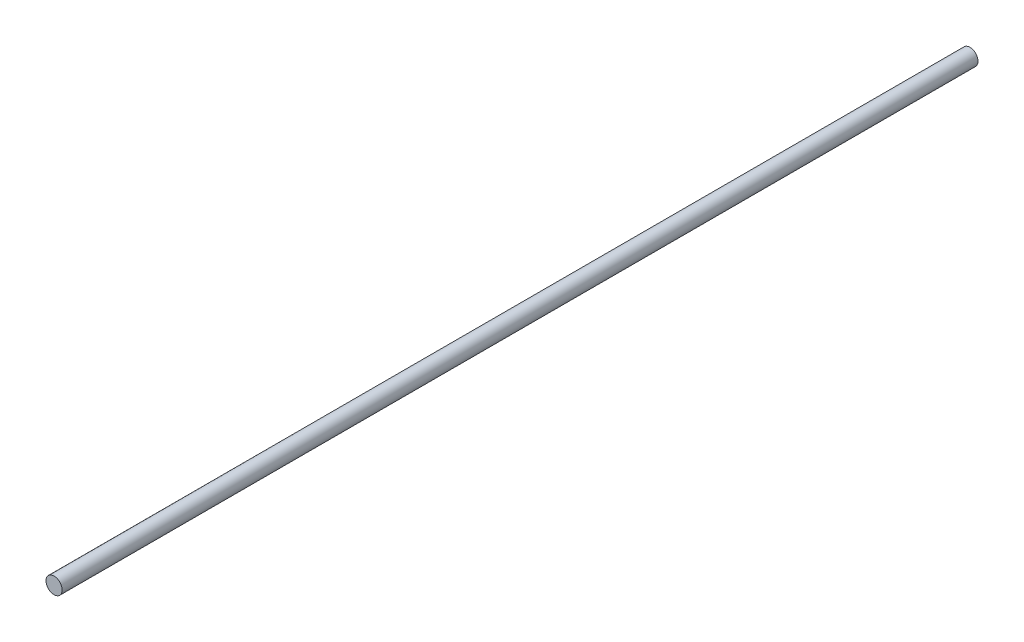
SolidWorks part; units mm, degrees
material "AISI 316 Annealed Stainless Steel Bar (SS)"
ref_plane "Front Plane" through (0, 0, 0) normal (0, 0, 1) x (1, 0, 0)
ref_plane "Top Plane" through (0, 0, 0) normal (0, 1, 0) x (1, 0, 0)
ref_plane "Right Plane" through (0, 0, 0) normal (1, 0, 0) x (0, 0, -1)
sketch "Sketch1" plane through (0, 0, 0) normal (0, 0, 1) x (1, 0, 0)
  circle A0 centre (0, 0) radius 1.5
  dimension "D1" = 3
extrude "Boss-Extrude1" add sketch "Sketch1" along normal mid plane 170
